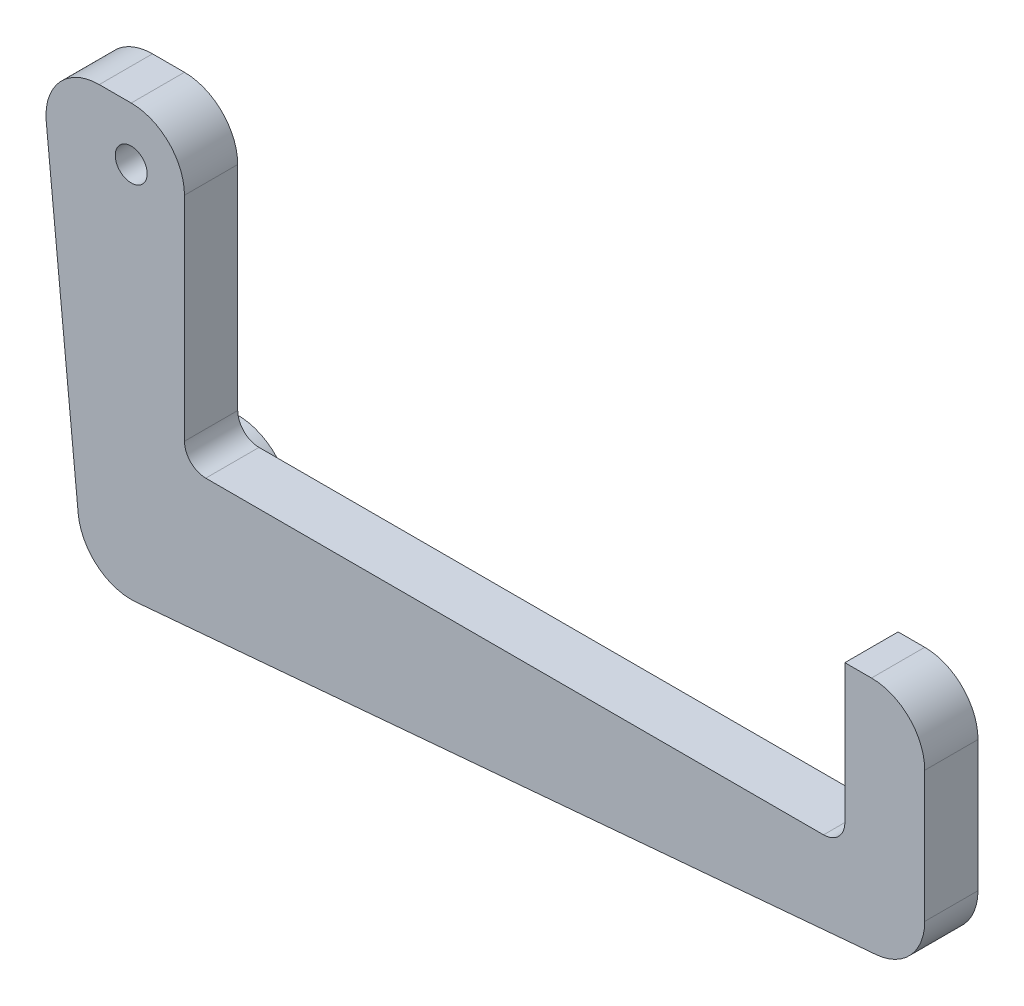
SolidWorks part; units mm, degrees
ref_plane "Front Plane" through (0, 0, 0) normal (0, 0, 1) x (1, 0, 0)
ref_plane "Top Plane" through (0, 0, 0) normal (0, 1, 0) x (1, 0, 0)
ref_plane "Right Plane" through (0, 0, 0) normal (1, 0, 0) x (0, 0, -1)
sketch "Sketch1" plane through (0, 0, 0) normal (0, 0, 1) x (1, 0, 0)
  line L0 (12.7, -10.16) -> (12.7, -48.7315)
  line L1 (19.6034, -55.0574) -> (107.8684, -47.3352)
  line L2 (113.665, -41.0094) -> (113.665, -25.4)
  line L3 (107.315, -19.05) -> (104.14, -19.05)
  line L4 (104.14, -19.05) -> (104.14, -35.56)
  line L5 (101.6, -38.1) -> (27.94, -38.1)
  line L6 (25.4, -35.56) -> (25.4, -10.16)
  arc A0 (12.7, -10.16) -> (19.05, -3.81) centre (19.05, -10.16) cw
  arc A1 (27.94, -38.1) -> (25.4, -35.56) centre (27.94, -35.56) cw
  arc A2 (104.14, -35.56) -> (101.6, -38.1) centre (101.6, -35.56) cw
  arc A3 (107.8684, -47.3352) -> (113.665, -41.0094) centre (107.315, -41.0094) ccw
  arc A4 (25.4, -10.16) -> (19.05, -3.81) centre (19.05, -10.16) ccw
  arc A5 (12.7, -48.7315) -> (19.6034, -55.0574) centre (19.05, -48.7315) ccw
  arc A6 (113.665, -25.4) -> (107.315, -19.05) centre (107.315, -25.4) ccw
  circle A7 centre (19.05, -10.16) radius 1.905
  point P11 (0, 0)
  point P14 (25.4, -38.1)
  point P17 (104.14, -38.1)
  point P22 (25.4, 0)
  dimension "D4" = 6.35
  dimension "D7" = 2.54
  dimension "D9" = 6.35
  dimension "D11" = 6.35
  dimension "D12" = 3.81
  dimension "D1" = 38.1
  dimension "D2" = 5
  dimension "D3" = 12.7
  dimension "D5" = 9.525
  dimension "D6" = 9.525
  dimension "D8" = 73.66
  dimension "D10" = 19.05
extrude "Boss-Extrude1" add sketch "Sketch1" along normal blind 6.35
ref_plane "Plane1" through (12.7, -48.7315, 6.35) normal (0, -1, 0) x (-1, 0, 0)
sketch "Sketch3" plane through (0, 0, 6.35) normal (0, 0, 1) x (1, 0, 0)
  circle A0 centre (19.05, -48.7315) radius 6.35
  arc A1 (12.7, -48.7315) -> (19.6034, -55.0574) centre (19.05, -48.7315) ccw construction
extrude "Boss-Extrude2" add sketch "Sketch3" against normal blind 12.7
sketch "Sketch6" plane through (0, 0, 6.35) normal (0, 0, 1) x (1, 0, 0)
  line L0 (12.7308, -49.3557) -> (8.9208, -10.7842)
  line L1 (15.24, -3.81) -> (19.05, -3.81)
  line L2 (12.7, -10.16) -> (12.7, -48.7315) construction
  line L3 (12.7, -10.16) -> (12.7, -48.7315)
  arc A0 (12.7, -48.7315) -> (19.6034, -55.0574) centre (19.05, -48.7315) ccw construction
  arc A1 (25.4, -10.16) -> (12.7, -10.16) centre (19.05, -10.16) ccw construction
  arc A2 (19.05, -3.81) -> (12.7, -10.16) centre (19.05, -10.16) ccw
  arc A3 (12.7, -48.7315) -> (12.7308, -49.3557) centre (19.05, -48.7315) ccw
  arc A4 (8.9208, -10.7842) -> (15.24, -3.81) centre (15.24, -10.16) cw
  dimension "D1" = 6.35
  dimension "D2" = 3.81
extrude "Boss-Extrude3" add sketch "Sketch6" against normal blind 6.35
